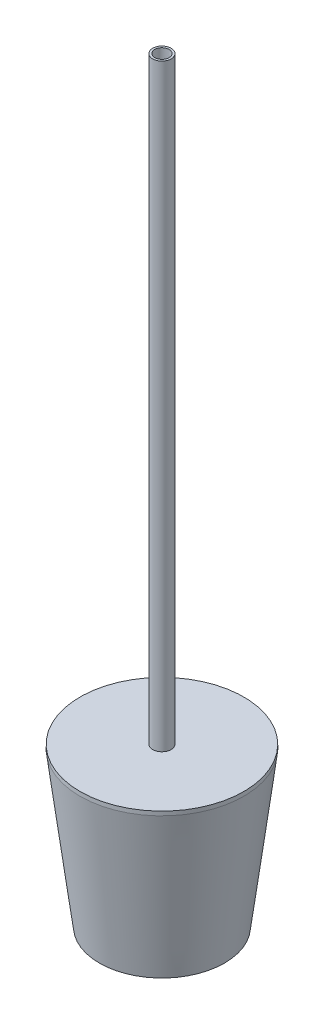
SolidWorks part; units mm, degrees
ref_plane "Front Plane" through (0, 0, 0) normal (0, 0, 1) x (1, 0, 0)
ref_plane "Top Plane" through (0, 0, 0) normal (0, 1, 0) x (1, 0, 0)
ref_plane "Right Plane" through (0, 0, 0) normal (1, 0, 0) x (0, 0, -1)
sketch "Sketch2" plane through (0, 0, 0) normal (0, 0, 1) x (1, 0, 0)
  line L0 (0, 0) -> (0, -50)
  line L1 (0, -50) -> (344.1391, -50)
  line L2 (0, 0) -> (300, 0)
  line L3 (0, -50) -> (0, 750) construction
  line L4 (300, 0) -> (400, 800)
  line L5 (344.1391, -50) -> (450.388, 799.9912)
  line L8 (400, 800) -> (450.388, 799.9912)
  dimension "D1" = 344.1391
  dimension "D2" = 50
  dimension "D3" = 300
  dimension "D4" = 800
  dimension "D5" = 97.125
  dimension "D6" = 262.875
  dimension "D7" = 800
revolve "Revolve1" add sketch "Sketch2" angle 360 about L3
ref_plane "Plane1" through (0, 797.56, 0) normal (0, 1, 0) x (1, 0, 0)
sketch "Sketch3" plane through (0, 797.56, 0) normal (0, 1, 0) x (1, 0, 0)
  circle A0 centre (0, 0) radius 450.388
  circle A1 centre (0, 0) radius 50.7743
extrude "Boss-Extrude1" add sketch "Sketch3" along normal blind 22.606
sketch "Sketch4" plane through (0, 797.56, 0) normal (0, 1, 0) x (1, 0, 0)
  circle A0 centre (0, 0) radius 50.8
  circle A1 centre (0, 0) radius 39.37
  dimension "D1" = 101.6
  dimension "D2" = 78.74
extrude "Boss-Extrude2" add sketch "Sketch4" along normal blind 3311.652 and the other way blind 330.2
